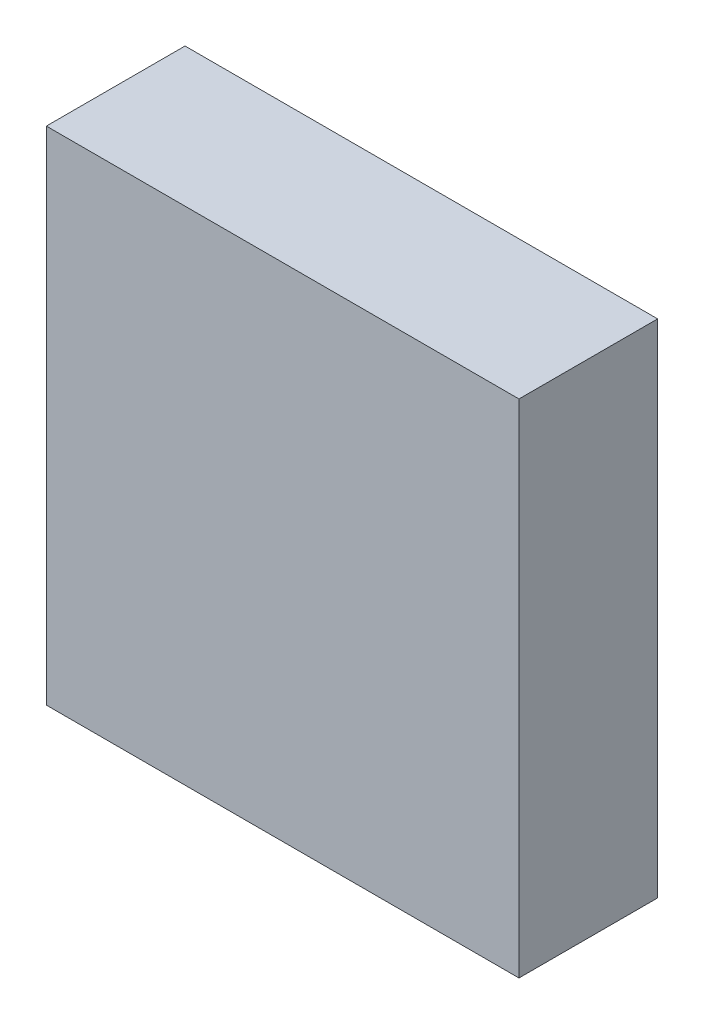
SolidWorks part; units mm, degrees
ref_plane "Front Plane" through (0, 0, 0) normal (0, 0, 1) x (1, 0, 0)
ref_plane "Top Plane" through (0, 0, 0) normal (0, 1, 0) x (1, 0, 0)
ref_plane "Right Plane" through (0, 0, 0) normal (1, 0, 0) x (0, 0, -1)
sketch "Sketch1" plane through (0, 0, 0) normal (0, 0, 1) x (1, 0, 0)
  line L0 (-1.704, 1.808) -> (1.704, 1.808)
  line L1 (1.704, 1.808) -> (1.704, -1.808)
  line L2 (1.704, -1.808) -> (-1.704, -1.808)
  line L3 (-1.704, -1.808) -> (-1.704, 1.808)
extrude "Component_Outline" add sketch "Sketch1" along normal blind 1 separate body
sketch3d "3DSketch1"
  line L0 (0, 0, 0) -> (1, 0, 0)
  line L1 (0, 0, 0) -> (0, 1, 0)
  line L2 (0, 0, 0) -> (0, 0, 1)
  point P0 (0, 0, 0)
